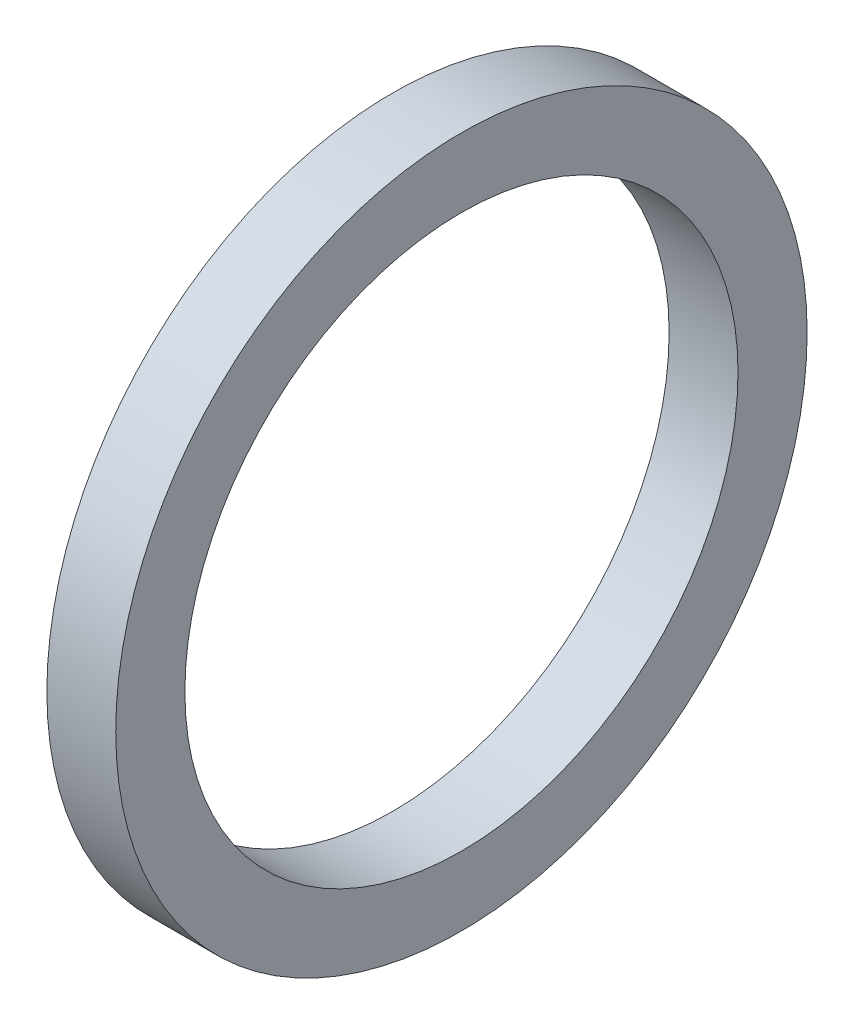
SolidWorks part; units mm, degrees
ref_plane "Front Plane" through (0, 0, 0) normal (0, 0, 1) x (1, 0, 0)
ref_plane "Top Plane" through (0, 0, 0) normal (0, 1, 0) x (1, 0, 0)
ref_plane "Right Plane" through (0, 0, 0) normal (1, 0, 0) x (0, 0, -1)
sketch "Sketch2" plane through (0, 0, 0) normal (0, 0, 1) x (1, 0, 0)
  line L0 (0, 0) -> (58.591, 0) construction
  line L2 (0, 0) -> (18.4, 0)
  line L3 (0, 0) -> (0, 2.5)
  line L4 (0, 2.5) -> (18.4, 2.5)
  line L5 (18.4, 0) -> (18.4, 2.5)
  line L6 (6.0094, 2.5) -> (6.0094, 6)
  line L11 (6.0094, 6) -> (9.9794, 6)
  line L16 (12.9794, 6) -> (12.9794, 3)
  line L17 (12.9794, 3) -> (13.6398, 3)
  line L18 (13.6398, 3) -> (13.6398, 2.5)
  line L19 (13.6398, 2.5) -> (6.0094, 2.5)
  line L22 (13.6398, 2.5) -> (16.1198, 2.5)
  line L23 (13.6398, 2.5) -> (13.6398, 4)
  line L24 (13.6398, 4) -> (16.1198, 4)
  line L25 (16.1198, 2.5) -> (16.1198, 4)
  line L27 (6.0094, 6) -> (9.9794, 6)
  line L28 (6.0094, 6) -> (6.0094, 9)
  line L29 (6.0094, 9) -> (9.9794, 9)
  line L30 (9.9794, 6) -> (9.9794, 9)
  line L31 (6.0094, 9) -> (6.0094, 8.25)
  line L32 (6.0094, 8.25) -> (5.0094, 8.25)
  line L33 (8.6609, 22.001) -> (8.6609, 12.476) construction
  line L34 (5.0094, 12.476) -> (12.3124, 12.476)
  line L35 (9.9794, 9) -> (12.3124, 9)
  line L36 (5.0094, 7.9375) -> (1.7709, 7.9375)
  line L37 (5.0094, 8.25) -> (5.0094, 12.476)
  line L38 (5.0094, 7.9375) -> (5.0094, 13.9365)
  line L39 (5.0094, 13.9365) -> (1.7709, 13.9365)
  line L40 (1.7709, 7.9375) -> (1.7709, 13.9365)
  line L41 (5.0094, 22.001) -> (12.3124, 22.001)
  line L42 (5.0094, 22.001) -> (5.0094, 30.1625)
  line L43 (5.0094, 30.1625) -> (12.3124, 30.1625)
  line L44 (12.3124, 22.001) -> (12.3124, 30.1625)
  line L49 (16.6398, 22.001) -> (16.6398, 7.5)
  line L51 (23.0198, 7.5) -> (23.0198, 6.5)
  line L54 (16.1198, 4) -> (13.6398, 4)
  line L56 (18.0398, 7.5) -> (23.0198, 7.5)
  line L57 (13.3124, 22.001) -> (16.6398, 22.001)
  line L58 (16.1198, 3.5) -> (20.0198, 3.5)
  line L59 (29.9098, 14) -> (26.9098, 11)
  line L60 (4.0094, 31.75) -> (18.0398, 31.75)
  line L61 (18.0398, 7.5) -> (23.0198, 7.5)
  line L62 (18.0398, 7.5) -> (18.0398, 12)
  line L63 (18.0398, 12) -> (23.0198, 12)
  line L64 (23.0198, 7.5) -> (23.0198, 12)
  line L65 (18.0398, 31.75) -> (18.0398, 12)
  line L66 (23.0198, 11) -> (26.9098, 11)
  line L67 (34.8098, 23) -> (31.3098, 19.5)
  line L68 (35.8098, 31) -> (38.7998, 33.99)
  line L69 (29.9098, 14) -> (29.9098, 15)
  line L70 (29.9098, 15) -> (22.9398, 15)
  line L71 (22.9398, 15) -> (21.0398, 15)
  line L72 (18.0398, 7.5) -> (16.6398, 7.5)
  line L73 (21.0398, 15) -> (21.0398, 43)
  line L74 (19.6115, 40) -> (9.6516, 40)
  line L75 (9.6516, 40) -> (4.0094, 40)
  line L76 (21.0398, 43) -> (19.6115, 43)
  line L77 (22.9398, 15) -> (29.9098, 15)
  line L78 (22.9398, 15) -> (22.9398, 21)
  line L79 (22.9398, 21) -> (29.9098, 21)
  line L80 (29.9098, 15) -> (29.9098, 21)
  line L81 (9.6516, 40) -> (19.6115, 40)
  line L82 (9.6516, 40) -> (9.6516, 50)
  line L83 (9.6516, 50) -> (19.6115, 50)
  line L84 (19.6115, 40) -> (19.6115, 50)
  line L85 (4.0094, 40) -> (4.0094, 31.75)
  line L86 (12.9794, 3) -> (12.9794, 2.5)
  line L87 (31.3098, 19.5) -> (29.9098, 19.5)
  line L88 (21.4694, 63.5) -> (21.4694, 51.308)
  line L89 (21.4694, 63.5) -> (25.9398, 63.5)
  line L90 (25.9398, 63.5) -> (25.9398, 25)
  line L91 (27.8398, 25) -> (25.9398, 25)
  line L92 (9.6516, 48) -> (8.2233, 48)
  line L93 (8.2233, 48) -> (8.2233, 53.476)
  line L94 (8.2233, 53.476) -> (19.6115, 53.476)
  line L95 (19.6115, 53.476) -> (19.6115, 50)
  line L96 (13.9174, 63.001) -> (13.9174, 53.476) construction
  line L97 (8.2233, 63.001) -> (19.6115, 63.001)
  line L98 (8.2233, 63.001) -> (8.2233, 68.2625)
  line L99 (8.2233, 68.2625) -> (19.6115, 68.2625)
  line L100 (19.6115, 63.001) -> (19.6115, 68.2625)
  line L101 (12.9794, 6) -> (11.9794, 6)
  line L102 (8.2233, 44.825) -> (4.9848, 44.825)
  line L103 (8.2233, 44.825) -> (8.2233, 54.9365)
  line L104 (8.2233, 54.9365) -> (4.9848, 54.9365)
  line L106 (9.9794, 6) -> (10.8794, 6)
  line L107 (27.8398, 25) -> (34.8098, 25)
  line L108 (34.8098, 25) -> (34.8098, 23)
  line L109 (0, 0) -> (-2, 0)
  line L110 (0, 0) -> (0, 11)
  line L111 (27.8398, 25) -> (34.8098, 25)
  line L112 (27.8398, 25) -> (27.8398, 32.5)
  line L113 (27.8398, 32.5) -> (34.8098, 32.5)
  line L114 (34.8098, 25) -> (34.8098, 32.5)
  line L115 (35.8098, 31) -> (34.8098, 31)
  line L116 (27.8398, 32.5) -> (27.8398, 64.5)
  line L117 (20.5849, 74.025) -> (6.2499, 74.025)
  line L118 (6.2499, 74.025) -> (6.2499, 76.2)
  line L119 (38.7998, 47.29) -> (30.8398, 55.25)
  line L120 (0, 11) -> (-2, 11)
  line L121 (38.7998, 43.815) -> (30.8623, 43.815)
  line L123 (-4.8152, 69.85) -> (1.5348, 76.2)
  line L124 (38.7998, 47.29) -> (38.7998, 33.99)
  line L125 (-2, 0) -> (-2, 11)
  line L126 (38.7998, 37.465) -> (30.8623, 37.465)
  line L127 (30.8623, 43.815) -> (30.8623, 37.465)
  line L128 (6.0094, 2.5) -> (6.0094, 0)
  line L129 (-0.0152, 63.5) -> (-0.0152, 30)
  line L132 (4.9848, 63.5) -> (-0.0152, 63.5)
  line L136 (-1.8152, 30) -> (-11.7752, 30)
  line L138 (-13.7752, 25.4) -> (-2, 25.4)
  line L139 (-2, 25.4) -> (-2, 11.5)
  line L140 (27.8398, 64.5) -> (20.5849, 64.5)
  line L141 (-1.8152, 30) -> (-11.7752, 30)
  line L142 (-1.8152, 30) -> (-1.8152, 39)
  line L143 (-1.8152, 39) -> (-11.7752, 39)
  line L144 (-11.7752, 30) -> (-11.7752, 39)
  line L145 (20.5849, 64.5) -> (20.5849, 74.025)
  line L146 (-12.7752, 37) -> (-12.7752, 47.29)
  line L147 (-12.7752, 37) -> (-11.7752, 37)
  line L148 (30.8398, 55.25) -> (30.8398, 76.2)
  line L149 (11.9794, 6) -> (11.9794, 5.45)
  line L154 (-2, 11.5) -> (0.5, 11.5)
  line L155 (4.9848, 60.6197) -> (24.0348, 60.6197)
  line L160 (4.9848, 60.6197) -> (4.9848, 55.8572)
  line L161 (4.9848, 55.8572) -> (24.0348, 55.8572)
  line L166 (24.0348, 60.6197) -> (24.0348, 55.8572)
  line L167 (4.9848, 60.6197) -> (24.0348, 55.8572) construction
  line L172 (4.9848, 55.8572) -> (24.0348, 60.6197) construction
  line L173 (24.0348, 62.2072) -> (25.9398, 62.2072)
  line L174 (11.9794, 5.45) -> (10.8794, 5.45)
  line L175 (10.8794, 6) -> (10.8794, 5.45)
  line L176 (24.0348, 62.2072) -> (24.0348, 54.2697)
  line L177 (24.0348, 54.2697) -> (25.9398, 54.2697)
  line L178 (25.9398, 62.2072) -> (25.9398, 54.2697)
  line L179 (24.0348, 62.2072) -> (25.9398, 54.2697) construction
  line L180 (24.0348, 54.2697) -> (25.9398, 62.2072) construction
  line L181 (3, 19.6197) -> (15.7, 19.6197)
  line L182 (3, 19.6197) -> (3, 14.8572)
  line L183 (3, 14.8572) -> (15.7, 14.8572)
  line L184 (15.7, 19.6197) -> (15.7, 14.8572)
  line L185 (3, 19.6197) -> (15.7, 14.8572) construction
  line L186 (3, 14.8572) -> (15.7, 19.6197) construction
  line L187 (15.7, 21.2072) -> (16.6398, 21.2072)
  line L188 (15.7, 21.2072) -> (15.7, 13.2697)
  line L189 (15.7, 13.2697) -> (16.6398, 13.2697)
  line L190 (16.6398, 21.2072) -> (16.6398, 13.2697)
  line L191 (15.7, 21.2072) -> (16.6398, 13.2697) construction
  line L192 (15.7, 13.2697) -> (16.6398, 21.2072) construction
  line L193 (0.5, 11.5) -> (0.5, 6.9375)
  line L194 (0.5, 6.9375) -> (1.7709, 6.9375)
  line L195 (23.0198, 6.5) -> (20.0198, 3.5)
  line L196 (4.9848, 63.5) -> (4.9848, 54.9365)
  line L197 (3, 43.825) -> (4.9848, 43.825)
  line L198 (1.7709, 6.9375) -> (1.7709, 7.9375)
  line L199 (6.0094, 0) -> (12.9794, 0)
  line L200 (12.9794, 0) -> (12.9794, 2.5)
  line L201 (18.0398, 31.75) -> (18.0398, 35.875)
  line L202 (18.0398, 35.875) -> (21.0398, 35.875)
  line L203 (30.8398, 76.2) -> (6.2499, 76.2)
  line L204 (2.8049, 69.85) -> (7.2499, 69.85) construction
  line L205 (7.2499, 67.4688) -> (26.2999, 67.4688)
  line L206 (7.2499, 74.025) -> (7.2499, 64.5)
  line L207 (7.2499, 64.5) -> (-1.8152, 64.5)
  line L208 (-1.8152, 64.5) -> (-1.8152, 39)
  line L209 (-12.7752, 47.29) -> (-4.8152, 55.25)
  line L210 (-4.8152, 55.25) -> (-4.8152, 69.85)
  line L211 (7.2499, 67.4688) -> (7.2499, 72.2312)
  line L212 (7.2499, 72.2312) -> (26.2999, 72.2313)
  line L213 (26.2999, 67.4688) -> (26.2999, 72.2313)
  line L214 (26.2999, 73.8187) -> (30.8398, 73.8187)
  line L215 (26.2999, 73.8187) -> (26.2999, 65.8813)
  line L216 (26.2999, 65.8813) -> (30.8398, 65.8813)
  line L217 (30.8398, 73.8187) -> (30.8398, 65.8813)
  line L218 (2.8049, 72.2313) -> (25.0299, 72.2313)
  line L219 (2.8049, 72.2313) -> (2.8049, 67.4687)
  line L220 (2.8049, 67.4687) -> (25.0299, 67.4687)
  line L221 (25.0299, 72.2313) -> (25.0299, 67.4687)
  line L222 (25.0299, 69.85) -> (20.5849, 69.85) construction
  line L223 (21.4694, 51.308) -> (22.9398, 51.308)
  line L224 (22.9398, 51.308) -> (22.9398, 21)
  line L225 (13.6398, 4) -> (13.6398, 12.2697)
  line L226 (13.6398, 12.2697) -> (13.3124, 12.2697)
  line L227 (13.3124, 12.2697) -> (13.3124, 22.001)
  line L228 (12.3124, 9) -> (12.3124, 12.476)
  line L229 (-1.8152, 30) -> (-0.0152, 30)
  line L230 (8.2233, 65.6317) -> (2.8049, 65.6317) construction
  line L231 (19.6115, 65.6317) -> (25.0299, 65.6317) construction
  line L232 (1.5348, 76.2) -> (6.2499, 76.2)
  line L233 (-11.7752, 30) -> (-13.7752, 30)
  line L234 (-13.7752, 30) -> (-13.7752, 25.4)
  line L235 (3, 13.9365) -> (3, 43.825)
  line L236 (4.9848, 54.9365) -> (4.9848, 44.825)
  line L237 (4.9848, 43.825) -> (4.9848, 44.825)
  circle A0 centre (26.8898, 25.95) radius 0.95
  circle A1 centre (21.9898, 15.95) radius 0.95
  circle A2 centre (17.3398, 8.2) radius 0.7
  circle A3 centre (10.4294, 6.45) radius 0.45
  circle A4 centre (-0.9152, 30.9) radius 0.9
  point P7 (24.9873, 58.2385)
  point P131 (16.1699, 17.2385)
  point P135 (14.5098, 58.2385)
  point P146 (9.35, 17.2385)
sketch "Sketch3" plane through (0, 0, 0) normal (0, 0, 1) x (1, 0, 0)
  line L0 (19.6115, 40) -> (9.6516, 40) construction
  line L1 (9.6516, 40) -> (9.6516, 50) construction
  line L2 (9.6516, 50) -> (19.6115, 50) construction
  line L3 (19.6115, 40) -> (19.6115, 50) construction
  line L4 (19.6115, 40) -> (9.6516, 40)
  line L5 (9.6516, 40) -> (9.6516, 50)
  line L6 (9.6516, 50) -> (19.6115, 50)
  line L7 (19.6115, 40) -> (19.6115, 50)
revolve "Revolve1" add sketch "Sketch3" angle 360 about L0
